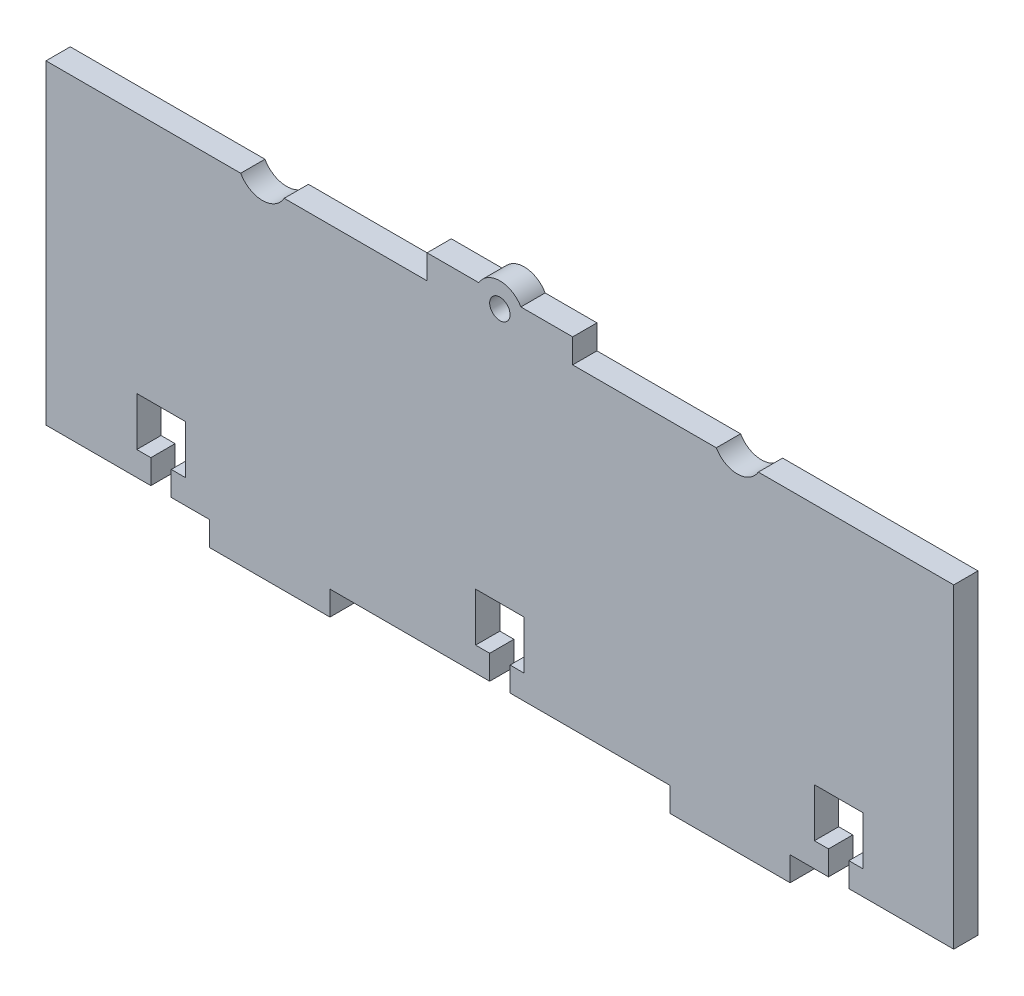
SolidWorks part; units mm, degrees
ref_plane "Front Plane" through (0, 0, 0) normal (0, 0, 1) x (1, 0, 0)
ref_plane "Top Plane" through (0, 0, 0) normal (0, 1, 0) x (1, 0, 0)
ref_plane "Right Plane" through (0, 0, 0) normal (1, 0, 0) x (0, 0, -1)
sketch "Sketch1" plane through (0, 0, 0) normal (0, 0, 1) x (1, 0, 0)
  line L0 (35, 0) -> (35, -5)
  line L1 (115, 0) -> (-115, 0)
  line L2 (0, 0) -> (0, 65) construction
  line L3 (115, 65) -> (-115, 65)
  line L4 (-115, 0) -> (-115, 65)
  line L5 (-115, 20) -> (-120, 20)
  line L6 (-115, 20) -> (-115, 45)
  line L7 (-115, 45) -> (-120, 45)
  line L8 (-120, 20) -> (-120, 45)
  line L9 (-100, 65) -> (-70, 65)
  line L10 (-100, 65) -> (-100, 70)
  line L11 (-100, 70) -> (-70, 70)
  line L12 (-70, 65) -> (-70, 70)
  line L13 (-95, 0) -> (-35, 0)
  line L14 (-95, 0) -> (-95, -5)
  line L15 (-95, -5) -> (-35, -5)
  line L16 (-35, 0) -> (-35, -5)
  line L17 (95, -5) -> (35, -5)
  line L18 (95, 0) -> (95, -5)
  line L19 (95, 0) -> (35, 0)
  line L20 (70, 65) -> (70, 70)
  line L21 (100, 70) -> (70, 70)
  line L22 (100, 65) -> (100, 70)
  line L23 (100, 65) -> (70, 65)
  line L24 (120, 20) -> (120, 45)
  line L25 (115, 45) -> (120, 45)
  line L26 (115, 20) -> (115, 45)
  line L27 (115, 20) -> (120, 20)
  line L28 (115, 0) -> (115, 65)
  point P9 (-120, 32.5)
  point P10 (0, 32.5)
  dimension "D1" = 115
  dimension "D2" = 65
  dimension "D3" = 5
  dimension "D4" = 25
  dimension "D5" = 30
  dimension "D6" = 15
  dimension "D7" = 5
  dimension "D8" = 5
  dimension "D9" = 60
  dimension "D10" = 20
extrude "Boss-Extrude1" add sketch "Sketch1" along normal blind 5 contours L1 L2 L3 L4 | L3 L22 L21 L20 | L18 L1 L0 L17 | L3 L12 L11 L10 | L16 L1 L14 L15 | L8 L5 L4 L7 | L26 L25 L24 L27
sketch "Sketch2" plane through (0, 0, 0) normal (0, 0, -1) x (-1, 0, 0)
  line L0 (120, 20) -> (120, 45) construction
  line L1 (85, -5) -> (120, -5)
  line L2 (85, -5) -> (85, 60)
  line L3 (85, 60) -> (120, 60)
  line L4 (120, -5) -> (120, 60)
  line L6 (95, -5) -> (35, -5) construction
  line L7 (0, 28.4281) -> (0, 15.5246) construction
  line L8 (-120, -5) -> (-120, 60)
  line L9 (-85, 60) -> (-120, 60)
  line L10 (-85, -5) -> (-85, 60)
  line L11 (-85, -5) -> (-120, -5)
  dimension "D1" = 35
  dimension "D2" = 35
  dimension "D3" = 65
extrude "Cut-Extrude1" cut sketch "Sketch2" against normal blind 10
sketch "Sketch4" plane through (0, 65, 0) normal (0, 1, 0) x (1, 0, 0)
  line L0 (51.2293, 0) -> (-51.2293, 0) construction
  line L1 (15, 0) -> (-15, 0)
  line L2 (15, 0) -> (15, -5)
  line L3 (15, -5) -> (-15, -5)
  line L4 (-15, 0) -> (-15, -5)
  line L5 (51.2293, -5) -> (-51.2293, -5) construction
  point P8 (0, 0)
  dimension "D1" = 30
  dimension "D2" = 15
extrude "Boss-Extrude2" add sketch "Sketch4" along normal blind 5
sketch "Sketch5" plane through (0, 0, 0) normal (0, 0, -1) x (-1, 0, 0)
  line L0 (-85, -5) -> (-35, -5) construction
  line L1 (-59.8, -5) -> (-79.8, -5)
  line L2 (-59.8, -5) -> (-59.8, 0)
  line L3 (-59.8, 0) -> (-79.8, 0)
  line L4 (-79.8, -5) -> (-79.8, 0)
  line L5 (-85, -5) -> (-85, 60) construction
  line L6 (0, 0) -> (0, 22.2278) construction
  line L7 (-35, 0) -> (35, 0) construction
  line L8 (79.8, -5) -> (79.8, 0)
  line L9 (59.8, 0) -> (79.8, 0)
  line L10 (59.8, -5) -> (59.8, 0)
  line L11 (59.8, -5) -> (79.8, -5)
  dimension "D1" = 20
  dimension "D2" = 5.2
extrude "Cut-Extrude3" cut sketch "Sketch5" against normal blind 5
sketch "Sketch6" plane through (0, 0, 0) normal (0, 0, -1) x (-1, 0, 0)
  line L0 (-15, 70) -> (15, 70) construction
  circle A0 centre (0, 67.5) radius 2.1
  dimension "D1" = 2.5
  dimension "D2" = 4.2
extrude "Cut-Extrude4" cut sketch "Sketch6" against normal blind 5
sketch "Sketch7" plane through (0, 0, 0) normal (0, 0, -1) x (-1, 0, 0)
  line L0 (-15, 70) -> (15, 70) construction
  line L1 (4.3301, 70) -> (-4.3301, 70)
  arc A0 (-4.3301, 70) -> (4.3301, 70) centre (0, 67.5) cw
  dimension "D1" = 5
extrude "Boss-Extrude3" add sketch "Sketch7" against normal blind 5
sketch "Sketch8" plane through (0, 0, 0) normal (0, 0, -1) x (-1, 0, 0)
  line L0 (79.8, 0) -> (59.8, 0) construction
  line L1 (67.7, 0) -> (71.9, 0)
  line L2 (67.7, 0) -> (67.7, 5)
  line L3 (67.7, 5) -> (71.9, 5)
  line L4 (71.9, 0) -> (71.9, 5)
  line L5 (0, 0) -> (0, 16.7932) construction
  line L6 (74.8, 5) -> (64.8, 5)
  line L7 (74.8, 5) -> (74.8, 15)
  line L8 (74.8, 15) -> (64.8, 15)
  line L9 (64.8, 5) -> (64.8, 15)
  line L10 (-64.8, 5) -> (-64.8, 15)
  line L11 (-74.8, 15) -> (-64.8, 15)
  line L12 (-74.8, 5) -> (-74.8, 15)
  line L13 (-74.8, 5) -> (-64.8, 5)
  line L14 (-71.9, 0) -> (-71.9, 5)
  line L15 (-67.7, 5) -> (-71.9, 5)
  line L16 (-67.7, 0) -> (-67.7, 5)
  line L17 (-67.7, 0) -> (-71.9, 0)
  line L18 (-35, 0) -> (35, 0) construction
  line L19 (-2.1, 0) -> (2.1, 0)
  line L20 (-2.1, 0) -> (-2.1, 5)
  line L21 (-2.1, 5) -> (2.1, 5)
  line L22 (2.1, 0) -> (2.1, 5)
  line L24 (-5, 5) -> (5, 5)
  line L25 (-5, 5) -> (-5, 15)
  line L26 (-5, 15) -> (5, 15)
  line L27 (5, 5) -> (5, 15)
  point P10 (69.8, 5)
  point P11 (69.8, 0)
  point P12 (69.8, 15)
  point P34 (0, 15)
  point P35 (0, 0)
  line M19 (-79.8, 0) -> (-59.8, 0)
  line M23 (-35, 0) -> (35, 0)
  line M27 (59.8, 0) -> (79.8, 0)
  dimension "D1" = 5
  dimension "D2" = 4.2
  dimension "D3" = 10
  dimension "D4" = 10
  dimension "D5" = 5
  dimension "D6" = 10
  dimension "D7" = 10
  dimension "D8" = 4.2
extrude "Cut-Extrude5" cut sketch "Sketch8" against normal blind 5 contours L12 L13 L10 L11 | L16 L13 L14 M19 | L5 L24 L27 L26 | L21 L5 L26 L25 L24 | L5 L19 L22 L24 | L5 L21 L20 M23 | L9 L6 L3 L7 L8 | L4 L3 L2 M27
sketch "Sketch10" plane through (0, 0, 0) normal (0, 0, -1) x (-1, 0, 0)
  line L0 (-100, 70) -> (-70, 70) construction
  line L1 (-115, 60) -> (-85, 60)
  line L2 (-115, 60) -> (-115, 70)
  line L3 (-115, 70) -> (-85, 70)
  line L4 (-85, 60) -> (-85, 70)
  line L5 (-115, 60) -> (-85, 70) construction
  line L6 (-115, 70) -> (-85, 60) construction
  line L7 (100, 70) -> (70, 70) construction
  line L8 (115, 60) -> (85, 60)
  line L9 (115, 60) -> (115, 70)
  line L10 (115, 70) -> (85, 70)
  line L11 (85, 60) -> (85, 70)
  line L12 (115, 60) -> (85, 70) construction
  line L13 (115, 70) -> (85, 60) construction
  point P4 (-100, 65)
  point P12 (100, 65)
extrude "Cut-Extrude7" cut sketch "Sketch10" against normal through all
sketch "Sketch11" plane through (0, 0, 0) normal (0, 0, -1) x (-1, 0, 0)
  line L1 (-70, 65) -> (-85, 65)
  line L2 (-70, 65) -> (-70, 70)
  line L3 (-70, 70) -> (-85, 70)
  line L4 (-85, 65) -> (-85, 70)
  line L5 (-70, 65) -> (-85, 70) construction
  line L6 (-70, 70) -> (-85, 65) construction
  line L7 (70, 65) -> (85, 65)
  line L8 (70, 65) -> (70, 70)
  line L9 (70, 70) -> (85, 70)
  line L10 (85, 65) -> (85, 70)
  line L11 (70, 65) -> (85, 70) construction
  line L12 (70, 70) -> (85, 65) construction
  line L13 (79.8, 0) -> (85, 0)
  line L14 (79.8, 0) -> (79.8, -5)
  line L15 (79.8, -5) -> (85, -5)
  line L16 (85, 0) -> (85, -5)
  line L17 (79.8, 0) -> (85, -5) construction
  line L18 (79.8, -5) -> (85, 0) construction
  line L19 (-79.8, 0) -> (-85, 0)
  line L20 (-79.8, 0) -> (-79.8, -5)
  line L21 (-79.8, -5) -> (-85, -5)
  line L22 (-85, 0) -> (-85, -5)
  line L23 (-79.8, 0) -> (-85, -5) construction
  line L24 (-79.8, -5) -> (-85, 0) construction
  point P4 (-77.5, 67.5)
  point P11 (77.5, 67.5)
  point P18 (82.4, -2.5)
  point P25 (-82.4, -2.5)
extrude "Cut-Extrude8" cut sketch "Sketch11" against normal through all
sketch "Sketch13" plane through (0, 0, 0) normal (0, 0, -1) x (-1, 0, 0)
  line L1 (-85, 65) -> (-93.5, 65)
  line L2 (-85, 65) -> (-85, 0)
  line L3 (-85, 0) -> (-93.5, 0)
  line L4 (-93.5, 65) -> (-93.5, 0)
  line L5 (-85, 65) -> (-93.5, 0) construction
  line L6 (-85, 0) -> (-93.5, 65) construction
  line L7 (85, 65) -> (93.5, 65)
  line L8 (85, 65) -> (85, 0)
  line L9 (85, 0) -> (93.5, 0)
  line L10 (93.5, 65) -> (93.5, 0)
  line L11 (85, 65) -> (93.5, 0) construction
  line L12 (85, 0) -> (93.5, 65) construction
  point P4 (-89.25, 32.5)
  point P11 (89.25, 32.5)
  dimension "D1" = 8.5
  dimension "D2" = 8.5
extrude "Boss-Extrude5" add sketch "Sketch13" against normal blind 5
sketch "Sketch14" plane through (0, 0, 0) normal (0, 0, -1) x (-1, 0, 0)
  circle A0 centre (-48.9151, 67.5) radius 5
  circle A1 centre (48.9151, 67.5) radius 5.1283
extrude "Cut-Extrude9" cut sketch "Sketch14" against normal blind 5
